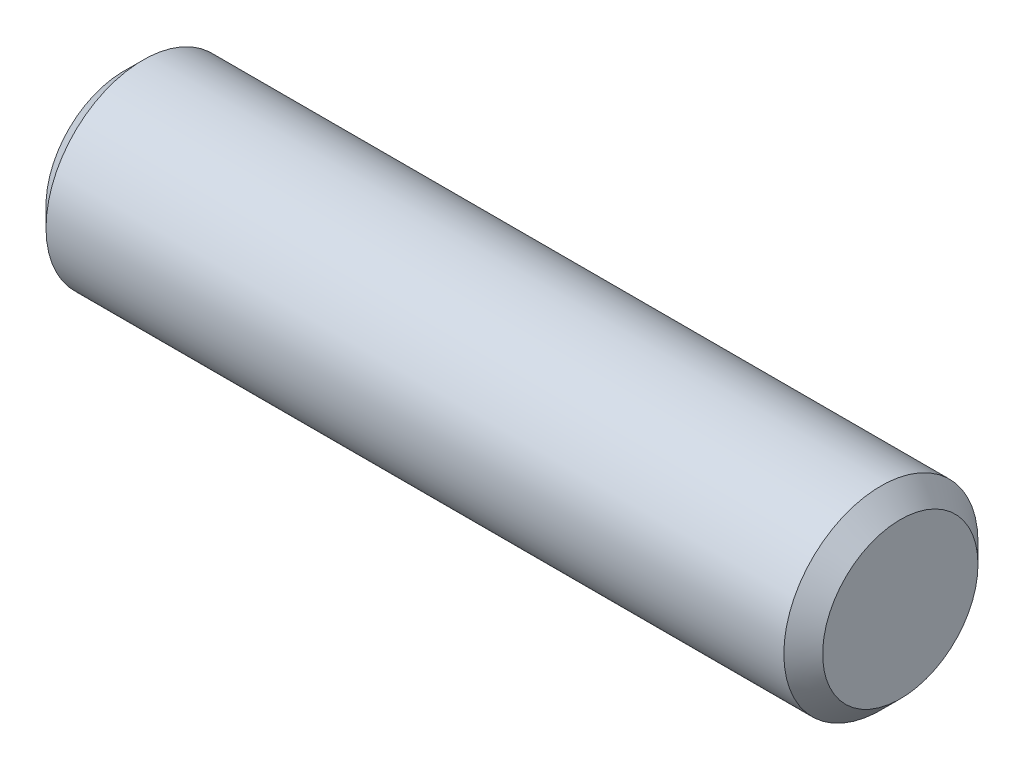
SolidWorks part; units mm, degrees
ref_plane "Front Plane" through (0, 0, 0) normal (0, 0, 1) x (1, 0, 0)
ref_plane "Top Plane" through (0, 0, 0) normal (0, 1, 0) x (1, 0, 0)
ref_plane "Right Plane" through (0, 0, 0) normal (1, 0, 0) x (0, 0, -1)
sketch "Sketch1" plane through (0, 0, 0) normal (0, 0, 1) x (1, 0, 0)
  line L0 (-3.175, 0) -> (3.175, 0) construction
  line L1 (-3.175, 0.7937) -> (-3.175, -0.7937) construction
  line L2 (3.175, 0.7937) -> (3.175, -0.7937) construction
  dimension "Diameter" = 1.5875
  dimension "Length" = 6.35
sketch "Sketch2" plane through (0, 0, 0) normal (1, 0, 0) x (0, 0, -1)
  circle A0 centre (0, 0) radius 0.7937
extrude "Extrude1" add sketch "Sketch2" against normal up to vertex (3.175 mm away) and the other way up to vertex (3.175 mm away) up to point (-3.175, 0, 0) other way up to point (3.175, 0, 0)
chamfer "Chamfer1" distance 0.1588 angle 45 2 edges at (3.175, 0, -0.7937) (-3.175, 0, -0.7937)
equation "\"D1@Chamfer1\" = \"Diameter@Sketch1\"*.1"
